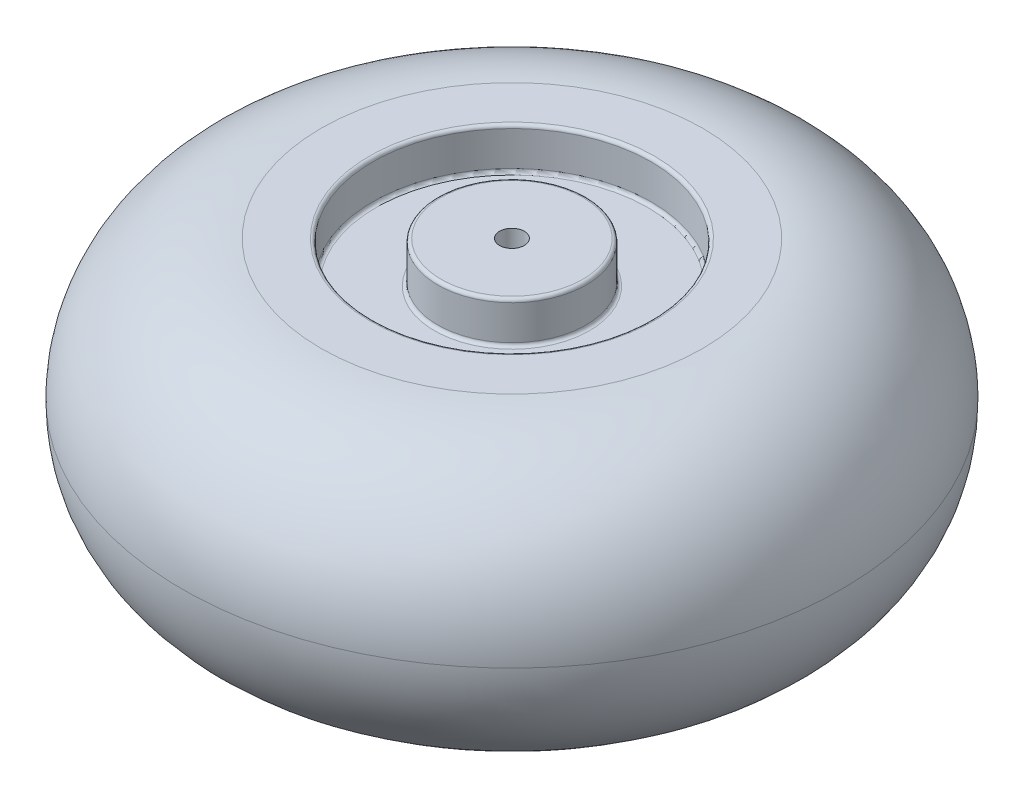
SolidWorks part; units mm, degrees
material "1060 Alloy"
ref_plane "Front Plane" through (0, 0, 0) normal (0, 0, 1) x (1, 0, 0)
ref_plane "Top Plane" through (0, 0, 0) normal (0, 1, 0) x (1, 0, 0)
ref_plane "Right Plane" through (0, 0, 0) normal (1, 0, 0) x (0, 0, -1)
sketch "Sketch3" plane through (0, 0, 0) normal (1, 0, 0) x (0, 0, -1)
  line L0 (0, 0) -> (0, 42.3409) construction
  line L1 (0, 0) -> (188.2619, 0) construction
  line L2 (6, -67.5) -> (6, 67.5)
  line L3 (6, 67.5) -> (34.3864, 67.5)
  line L4 (36, 65.8864) -> (36, 49.1136)
  line L5 (37.6136, 47.5) -> (65.9196, 47.5)
  line L6 (67.5332, 49.1136) -> (67.5332, 65.8864)
  line L7 (69.1468, 67.5) -> (92.5332, 67.5)
  line L8 (69.1468, -67.5) -> (92.5332, -67.5)
  line L9 (67.5332, -49.1136) -> (67.5332, -65.8864)
  line L10 (37.6136, -47.5) -> (65.9196, -47.5)
  line L11 (36, -65.8864) -> (36, -49.1136)
  line L12 (6, -67.5) -> (34.3864, -67.5)
  arc A0 (92.5332, 67.5) -> (159.8573, 0) centre (92.5332, 0.1756) cw
  arc A1 (92.5332, -67.5) -> (159.8573, 0) centre (92.5332, -0.1756) ccw
  arc A2 (69.1468, -67.5) -> (67.5332, -65.8864) centre (69.1468, -65.8864) cw
  arc A3 (67.5332, -49.1136) -> (65.9196, -47.5) centre (65.9196, -49.1136) ccw
  arc A4 (37.6136, -47.5) -> (36, -49.1136) centre (37.6136, -49.1136) ccw
  arc A5 (36, -65.8864) -> (34.3864, -67.5) centre (34.3864, -65.8864) cw
  arc A6 (67.5332, 65.8864) -> (69.1468, 67.5) centre (69.1468, 65.8864) cw
  arc A7 (65.9196, 47.5) -> (67.5332, 49.1136) centre (65.9196, 49.1136) ccw
  arc A8 (34.3864, 67.5) -> (36, 65.8864) centre (34.3864, 65.8864) cw
  arc A9 (36, 49.1136) -> (37.6136, 47.5) centre (37.6136, 49.1136) ccw
  point P15 (6, 0)
  point P23 (67.5332, -67.5)
  point P26 (67.5332, -47.5)
  point P29 (36, -47.5)
  point P32 (36, -67.5)
  point P35 (67.5332, 67.5)
  point P38 (67.5332, 47.5)
  point P41 (36, 67.5)
  point P44 (36, 47.5)
  dimension "D9" = 67.3244
  dimension "D1" = 6
  dimension "D2" = 30
  dimension "D3" = 67.5
  dimension "D4" = 25
  dimension "D5" = 20
  dimension "D6" = 20
  dimension "D7" = 28.306
  dimension "D8" = 1.6136
revolve "Revolve1" add sketch "Sketch3" angle 360 about L0
equation "\"wheelShaftDiameter\"= 12mm"
equation "\"D1@Sketch3\"=\"wheelShaftDiameter\"/2"
equation "\"wheelThickness\"= 135mm"
equation "\"D3@Sketch3\"=\"wheelThickness\"/2"
